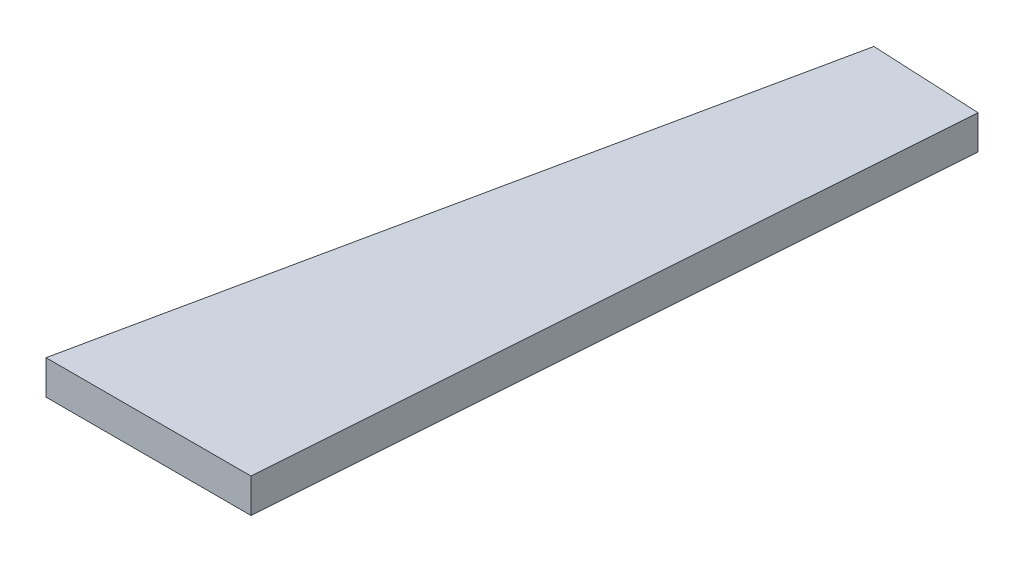
SolidWorks part; units mm, degrees
ref_plane "Front Plane" through (0, 0, 0) normal (0, 0, 1) x (1, 0, 0)
ref_plane "Top Plane" through (0, 0, 0) normal (0, 1, 0) x (1, 0, 0)
ref_plane "Right Plane" through (0, 0, 0) normal (1, 0, 0) x (0, 0, -1)
sketch "Sketch1" plane through (0, 0, 0) normal (0, 1, 0) x (1, 0, 0)
  line L0 (406.4, -19.507) -> (225.291, -2540)
  line L5 (-536.709, -2540) -> (225.291, -2540)
  line L7 (-536.709, -2540) -> (0, 0)
  line L8 (0, 0) -> (406.4, -19.507)
  point P2 (0, 0)
  point P3 (0, 0)
  dimension "D1" = 406.4
  dimension "D2" = 762
  dimension "D3" = 2540
extrude "Boss-Extrude1" add sketch "Sketch1" along normal mid plane 127
